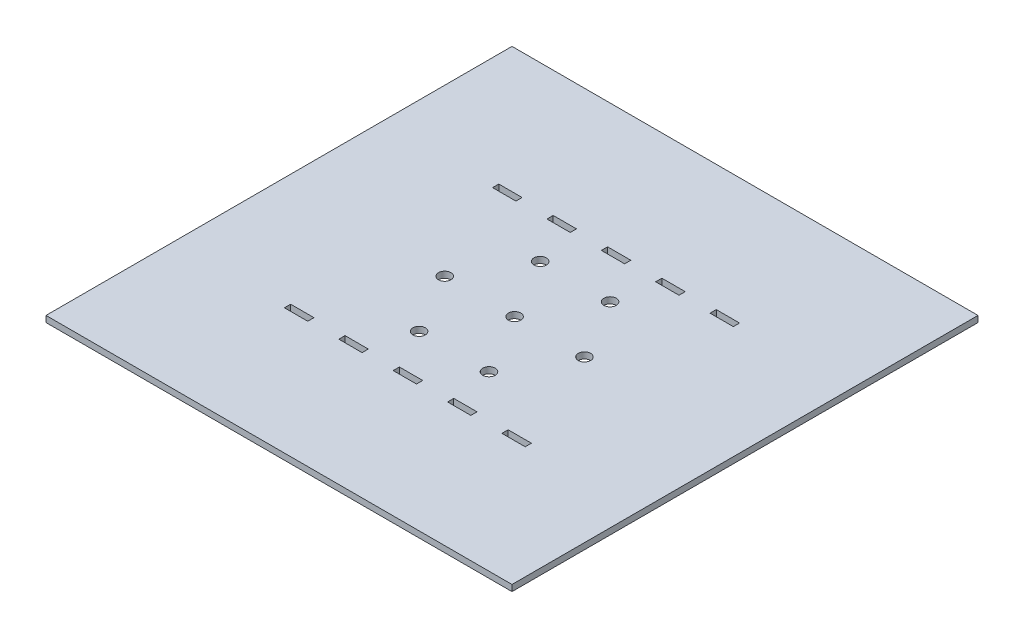
SolidWorks part; units mm, degrees
material "1060 Alloy"
ref_plane "Front Plane" through (0, 0, 0) normal (0, 0, 1) x (1, 0, 0)
ref_plane "Top Plane" through (0, 0, 0) normal (0, 1, 0) x (1, 0, 0)
ref_plane "Right Plane" through (0, 0, 0) normal (1, 0, 0) x (0, 0, -1)
sketch "Sketch1" plane through (0, 0, 0) normal (0, 1, 0) x (1, 0, 0)
  line L0 (-101.4767, -0.1764) -> (-43.8253, -0.1764) construction
  line L5 (-78.9767, 68.8236) -> (-63.9767, 68.8236)
  line L6 (-78.9767, 68.8236) -> (-78.9767, 64.8236)
  line L7 (-78.9767, 64.8236) -> (-63.9767, 64.8236)
  line L8 (-63.9767, 68.8236) -> (-63.9767, 64.8236)
  line L9 (-43.9767, 68.8236) -> (-28.9767, 68.8236)
  line L10 (-43.9767, 68.8236) -> (-43.9767, 64.8236)
  line L11 (-43.9767, 64.8236) -> (-28.9767, 64.8236)
  line L12 (-28.9767, 68.8236) -> (-28.9767, 64.8236)
  line L13 (-8.9767, 68.8236) -> (6.0233, 68.8236)
  line L14 (-8.9767, 68.8236) -> (-8.9767, 64.8236)
  line L15 (-8.9767, 64.8236) -> (6.0233, 64.8236)
  line L16 (6.0233, 68.8236) -> (6.0233, 64.8236)
  line L17 (26.0233, 68.8236) -> (41.0233, 68.8236)
  line L18 (26.0233, 68.8236) -> (26.0233, 64.8236)
  line L19 (26.0233, 64.8236) -> (41.0233, 64.8236)
  line L20 (41.0233, 68.8236) -> (41.0233, 64.8236)
  line L21 (61.0233, 68.8236) -> (76.0233, 68.8236)
  line L22 (61.0233, 68.8236) -> (61.0233, 64.8236)
  line L23 (61.0233, 64.8236) -> (76.0233, 64.8236)
  line L24 (76.0233, 68.8236) -> (76.0233, 64.8236)
  line L25 (76.0233, -69.1764) -> (76.0233, -65.1764)
  line L26 (61.0233, -65.1764) -> (76.0233, -65.1764)
  line L27 (61.0233, -69.1764) -> (61.0233, -65.1764)
  line L28 (61.0233, -69.1764) -> (76.0233, -69.1764)
  line L29 (41.0233, -69.1764) -> (41.0233, -65.1764)
  line L30 (26.0233, -65.1764) -> (41.0233, -65.1764)
  line L31 (26.0233, -69.1764) -> (26.0233, -65.1764)
  line L32 (26.0233, -69.1764) -> (41.0233, -69.1764)
  line L33 (6.0233, -69.1764) -> (6.0233, -65.1764)
  line L34 (-8.9767, -65.1764) -> (6.0233, -65.1764)
  line L35 (-8.9767, -69.1764) -> (-8.9767, -65.1764)
  line L36 (-8.9767, -69.1764) -> (6.0233, -69.1764)
  line L37 (-28.9767, -69.1764) -> (-28.9767, -65.1764)
  line L38 (-43.9767, -65.1764) -> (-28.9767, -65.1764)
  line L39 (-43.9767, -69.1764) -> (-43.9767, -65.1764)
  line L40 (-43.9767, -69.1764) -> (-28.9767, -69.1764)
  line L41 (-63.9767, -69.1764) -> (-63.9767, -65.1764)
  line L42 (-78.9767, -65.1764) -> (-63.9767, -65.1764)
  line L43 (-78.9767, -69.1764) -> (-78.9767, -65.1764)
  line L44 (-78.9767, -69.1764) -> (-63.9767, -69.1764)
  line L45 (43.8253, -0.1764) -> (98.5233, -0.1764) construction
  line L46 (-22.5, 38.9711) -> (-20.5, 35.507) construction
  line L47 (22.5, -38.9711) -> (24.5, -35.507) construction
  line L48 (45, 0) -> (3, 0) construction
  line L49 (-45, 0) -> (-41.5359, 2) construction
  line L50 (22.5, 38.9711) -> (20.5, 35.507) construction
  line L51 (19.0359, 36.9711) -> (22.5, 38.9711) construction
  line L52 (43, -3.4641) -> (45, 0) construction
  line L53 (1.5, 2.5981) -> (-1.5, -2.5981) construction
  line L54 (4, 0) -> (-4, 0) construction
  line L55 (1.5, -2.5981) -> (22.5, -38.9711) construction
  line L56 (-20.5, -35.507) -> (-22.5, -38.9711) construction
  line L57 (-41, 0) -> (-45, 0) construction
  line L58 (-2, 3.4641) -> (2, -3.4641) construction
  line L60 (-151.4767, 149.8236) -> (148.5233, 149.8236)
  line L61 (-151.4767, 149.8236) -> (-151.4767, -150.1764)
  line L62 (-151.4767, -150.1764) -> (148.5233, -150.1764)
  line L63 (148.5233, 149.8236) -> (148.5233, -150.1764)
  circle A1 centre (0, 0) radius 4
  circle A2 centre (45, 0) radius 4
  circle A3 centre (22.5, 38.9711) radius 4
  circle A4 centre (-22.5, 38.9711) radius 4
  circle A5 centre (-45, 0) radius 4
  circle A6 centre (-22.5, -38.9711) radius 4
  circle A7 centre (22.5, -38.9711) radius 4
  point P83 (148.5233, -0.1764)
  dimension "D20" = 90
  dimension "D21" = 90
  dimension "D23" = 8
  dimension "D26" = 8
  dimension "D28" = 0.1764
  dimension "D3" = 15
  dimension "D4" = 4
  dimension "D5" = 4
  dimension "D6" = 4
  dimension "D7" = 4
  dimension "D8" = 4
  dimension "D9" = 15
  dimension "D10" = 15
  dimension "D11" = 15
  dimension "D12" = 15
  dimension "D13" = 65
  dimension "D15" = 20
  dimension "D16" = 20
  dimension "D17" = 20
  dimension "D18" = 20
  dimension "D22" = 90
  dimension "D24" = 45
  dimension "D25" = 45
  dimension "D27" = 45
  dimension "D29" = 300
  dimension "D30" = 300
extrude "Boss-Extrude1" add sketch "Sketch1" along normal blind 4
